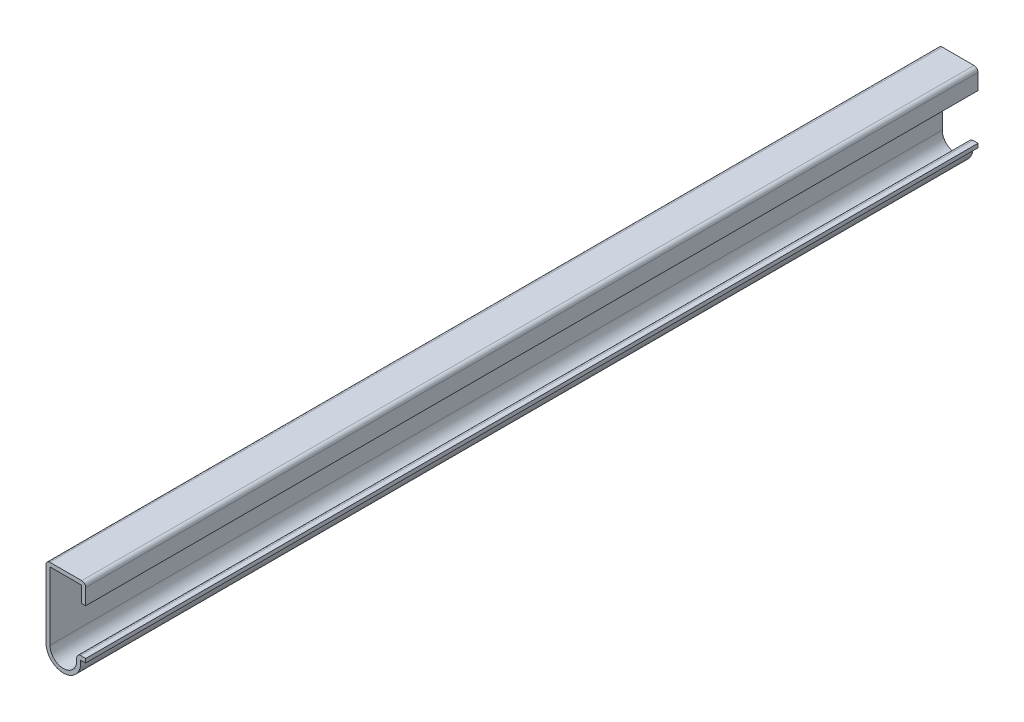
SolidWorks part; units mm, degrees
ref_plane "Front Plane" through (0, 0, 0) normal (0, 0, 1) x (1, 0, 0)
ref_plane "Top Plane" through (0, 0, 0) normal (0, 1, 0) x (1, 0, 0)
ref_plane "Right Plane" through (0, 0, 0) normal (1, 0, 0) x (0, 0, -1)
sketch "Sketch1" plane through (0, 0, 0) normal (0, 0, 1) x (1, 0, 0)
  line L0 (0, 0) -> (-1.5875, 0)
  line L1 (-12.7, -0.7938) -> (-12.7, 22.225)
  line L2 (-12.7, 22.225) -> (0, 22.225)
  line L3 (0, 22.225) -> (0, 15.875)
  line L4 (-1.5875, 0) -> (-1.5875, -0.7938)
  arc A0 (-1.5875, -0.7938) -> (-12.7, -0.7938) centre (-7.1437, -0.7938) cw
  dimension "D5" = 6.35
  dimension "D1" = 11.1125
  dimension "D2" = 1.5875
  dimension "D3" = 28.575
  dimension "D4" = 6.35
extrude "Extrude-Thin1" add sketch "Sketch1" against normal blind 285.75 thin
fillet "Fillet1" radius 1.27 3 edges at (0, 22.225, -142.875) (-12.7, 22.225, -142.875) (-2.8575, 1.27, -142.875)
